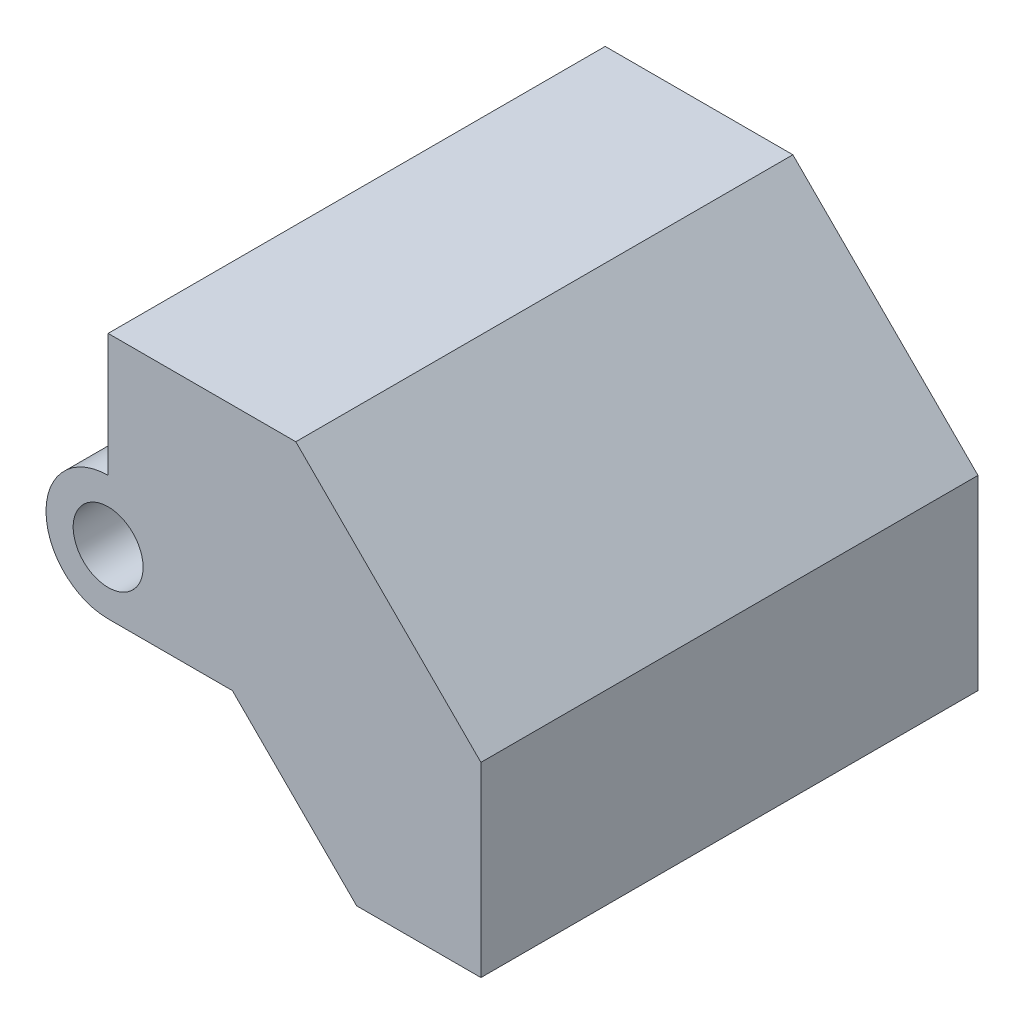
SolidWorks part; units mm, degrees
ref_plane "Front Plane" through (0, 0, 0) normal (0, 0, 1) x (1, 0, 0)
ref_plane "Top Plane" through (0, 0, 0) normal (0, 1, 0) x (1, 0, 0)
ref_plane "Right Plane" through (0, 0, 0) normal (1, 0, 0) x (0, 0, -1)
sketch "Sketch1" plane through (0, 0, 0) normal (0, 0, 1) x (1, 0, 0)
  line L0 (-6.273, -0.4871) -> (6.427, -0.4871)
  line L1 (6.427, -0.4871) -> (19.127, -13.1871)
  line L2 (19.127, -13.1871) -> (31.827, -13.1871)
  line L3 (31.827, -13.1871) -> (31.827, 5.8629)
  line L4 (-6.273, 24.7817) -> (-6.273, 12.2129)
  line L6 (31.827, 5.8629) -> (12.9082, 24.7817)
  line L7 (12.9082, 24.7817) -> (-6.273, 24.7817)
  line L8 (-6.273, 12.2129) -> (-6.273, -13.1871)
  circle A0 centre (-6.273, 5.8629) radius 6.35
  dimension "D1" = 12.7
  dimension "D2" = 25.4
  dimension "D3" = 12.7
  dimension "D4" = 12.7
  dimension "D5" = 12.7
  dimension "D6" = 12.7
extrude "Boss-Extrude1" add sketch "Sketch1" against normal blind 50.8 contours A0 L0 L1 L2 L3 L6 L7 L4 | L8 A0 | L8 A0
hole_wizard "9/32 (0.28125) Diameter Hole1" positions "3DSketch1" profile "Sketch2" hole size "9/32" standard "ANSI Inch" end condition through all
sketch3d "3DSketch1"
  line L0 (-6.273, 5.8629, -50.8) -> (-6.273, 5.8629, 0) construction
  point P0 (-6.273, 5.8629, 0)
sketch "Sketch2" plane through (-6.273, 5.8629, 0) normal (1, 0, 0) x (0, -1, 0)
  line L0 (0, 0) -> (0, 50.8)
  line L1 (0, 50.8) -> (3.5719, 50.8)
  line L2 (3.5719, 50.8) -> (3.5719, 0)
  line L5 (3.5719, 0) -> (0, 0)
  line L11 (0, -6.35) -> (0, 107.95) construction
  dimension "Thru Hole Dia." = 7.1437
  dimension "Thru Hole Depth" = 50.8
